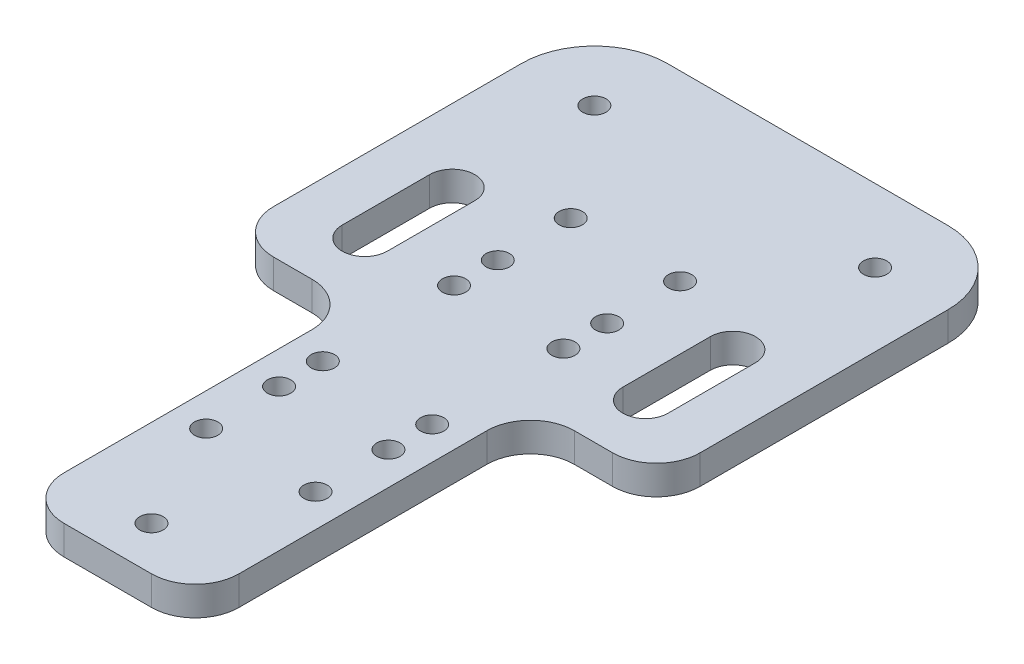
SolidWorks part; units mm, degrees
ref_plane "Front Plane" through (0, 0, 0) normal (0, 0, 1) x (1, 0, 0)
ref_plane "Top Plane" through (0, 0, 0) normal (0, 1, 0) x (1, 0, 0)
ref_plane "Right Plane" through (0, 0, 0) normal (1, 0, 0) x (0, 0, -1)
sketch "Sketch1" plane through (0, 0, 0) normal (0, 1, 0) x (1, 0, 0)
  line L0 (-19.25, 20.5) -> (-19.25, 8.5) construction
  line L1 (-8, 40) -> (8, 40) construction
  line L2 (-8, 40) -> (-8, -40) construction
  line L3 (-8, -40) -> (8, -40) construction
  line L4 (8, 40) -> (8, -40) construction
  line L5 (0, -40) -> (0, 40) construction
  line L6 (-8, 0) -> (8, 0) construction
  line L7 (-19.25, 57) -> (19.25, 57) construction
  line L8 (-19.25, 57) -> (-19.25, 23) construction
  line L9 (-19.25, 23) -> (19.25, 23) construction
  line L10 (19.25, 57) -> (19.25, 23) construction
  line L11 (0, 23) -> (0, 57) construction
  line L12 (-19.25, 40) -> (19.25, 40) construction
  line L13 (-16.15, 20.5) -> (-16.15, 8.5)
  line L14 (-22.35, 20.5) -> (-22.35, 8.5)
  line L15 (19.25, 20.5) -> (19.25, 8.5) construction
  line L16 (16.15, 20.5) -> (16.15, 8.5)
  line L17 (22.35, 20.5) -> (22.35, 8.5)
  line L18 (-29.25, 40) -> (-29.25, 0)
  line L19 (-7.5, 25) -> (7.5, 25) construction
  line L20 (-7.5, 25) -> (-7.5, 15) construction
  line L21 (-7.5, 15) -> (7.5, 15) construction
  line L22 (7.5, 25) -> (7.5, 15) construction
  line L23 (0, 15) -> (0, 25) construction
  line L24 (-7.5, 20) -> (7.5, 20) construction
  line L25 (-7.5, 15) -> (7.5, 15) construction
  line L26 (-7.5, 15) -> (-7.5, 9) construction
  line L27 (-7.5, 9) -> (7.5, 9) construction
  line L28 (7.5, 15) -> (7.5, 9) construction
  line L29 (0, 9) -> (0, 15) construction
  line L30 (-7.5, 12) -> (7.5, 12) construction
  line L31 (-29.25, 0) -> (-12, 0)
  line L32 (-12, 0) -> (-12, -46)
  line L33 (-19.25, 50) -> (19.25, 50)
  line L34 (-12, -46) -> (12, -46)
  line L35 (12, 0) -> (12, -46)
  line L36 (29.25, 0) -> (12, 0)
  line L37 (29.25, 40) -> (29.25, 0)
  circle A0 centre (0, -40) radius 8 construction
  circle A1 centre (-19.25, 40) radius 17 construction
  circle A2 centre (19.25, 40) radius 17 construction
  circle A3 centre (-19.25, 15.5) radius 7.5 construction
  circle A4 centre (19.25, 15.5) radius 7.5 construction
  arc A5 (-16.15, 20.5) -> (-22.35, 20.5) centre (-19.25, 20.5) ccw
  arc A6 (-22.35, 8.5) -> (-16.15, 8.5) centre (-19.25, 8.5) ccw
  arc A7 (16.15, 20.5) -> (22.35, 20.5) centre (19.25, 20.5) cw
  arc A8 (22.35, 8.5) -> (16.15, 8.5) centre (19.25, 8.5) cw
  circle A9 centre (-19.25, 40) radius 1.6
  circle A10 centre (19.25, 40) radius 1.6
  circle A11 centre (0, -40) radius 1.6
  circle A12 centre (-7.5, 25) radius 1.6
  circle A13 centre (7.5, 25) radius 1.6
  circle A14 centre (7.5, 15) radius 1.6
  circle A15 centre (-7.5, 15) radius 1.6
  circle A16 centre (-7.5, 9) radius 1.6
  circle A17 centre (7.5, 9) radius 1.6
  arc A18 (-29.25, 40) -> (-19.25, 50) centre (-19.25, 40) cw
  circle A19 centre (7.5, -9) radius 1.6
  circle A20 centre (-7.5, -9) radius 1.6
  circle A21 centre (7.5, -15) radius 1.6
  circle A22 centre (-7.5, -15) radius 1.6
  circle A23 centre (7.5, -25) radius 1.6
  circle A24 centre (-7.5, -25) radius 1.6
  arc A25 (29.25, 40) -> (19.25, 50) centre (19.25, 40) ccw
  point P0 (0, 0)
  point P16 (-19.25, 14.5)
  point P25 (19.25, 14.5)
  point P31 (0, 20)
  point P51 (0, 0)
  point P52 (0, 0)
  point P65 (0, 0)
  point P67 (0, -46)
  point P71 (0, 50)
  point P339 (0, 12)
  dimension "D5" = 15
  dimension "D6" = 3.1
  dimension "D9" = 3.2
  dimension "D14" = 3.2
  dimension "D1" = 16
  dimension "D2" = 80
  dimension "D3" = 38.5
  dimension "D4" = 34
  dimension "D7" = 5
  dimension "D8" = 12
  dimension "D10" = 10
  dimension "D11" = 15
  dimension "D12" = 15
  dimension "D13" = 6
  dimension "D16" = 10
  dimension "D17" = 12
  dimension "D18" = 6
extrude "Boss-Extrude1" add sketch "Sketch1" along normal blind 4
fillet "Fillet1" radius 6 6 edges at (12, 2, 0) (-12, 2, 0) (29.25, 2, 0) (12, 2, 46) (-12, 2, 46) (-29.25, 2, 0)
